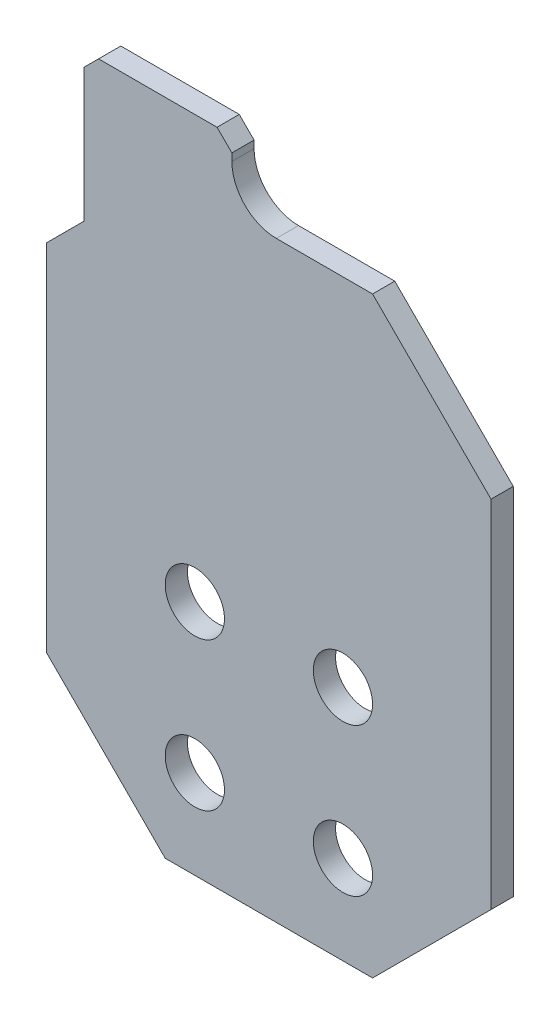
SolidWorks part; units mm, degrees
material "1060 Alloy"
ref_plane "Front Plane" through (0, 0, 0) normal (0, 0, 1) x (1, 0, 0)
ref_plane "Top Plane" through (0, 0, 0) normal (0, 1, 0) x (1, 0, 0)
ref_plane "Right Plane" through (0, 0, 0) normal (1, 0, 0) x (0, 0, -1)
sketch "Sketch1" plane through (0, 0, 0) normal (0, 0, 1) x (1, 0, 0)
  line L0 (20, -34) -> (10, -34) construction
  line L1 (0, 0) -> (30, 0)
  line L2 (0, 0) -> (0, -40)
  line L3 (0, -40) -> (30, -40)
  line L4 (30, 0) -> (30, -40)
  line L5 (10, -34) -> (15, -34) construction
  line L6 (15, -34) -> (15, -40) construction
  circle A0 centre (20, -34) radius 2
  circle A1 centre (10, -34) radius 2
  circle A2 centre (20, -24) radius 2
  circle A3 centre (10, -24) radius 2
  dimension "D1" = 4
  dimension "D2" = 4
  dimension "D3" = 6
  dimension "D4" = 10
  dimension "D5" = 40
  dimension "D6" = 30
  dimension "D7" = 10
extrude "Boss-Extrude1" add sketch "Sketch1" along normal blind 1.5
chamfer "Chamfer1" distance 8 angle 45 4 edges at (0, -40, 0.75) (30, -40, 0.75) (30, 0, 0.75) (0, 0, 0.75)
sketch "Sketch2" plane through (0, 0, 1.5) normal (0, 0, 1) x (1, 0, 0)
  line L0 (2.5, -5.5) -> (2.5, 4.5)
  line L1 (8, 0) -> (0, -8) construction
  line L2 (2.5, 4.5) -> (12.5, 4.5)
  line L3 (12.5, 4.5) -> (12.5, -5.5)
  line L4 (12.5, -5.5) -> (2.5, -5.5)
  dimension "D1" = 2.5
  dimension "D2" = 10
  dimension "D3" = 10
extrude "Boss-Extrude2" add sketch "Sketch2" against normal blind 1.5
ref_plane "Plane1" through (15, 0, 0) normal (1, 0, 0) x (0, 0, -1)
chamfer "Chamfer3" distance 1 angle 45 2 edges at (12.5, 4.5, 0.75) (2.5, 4.5, 0.75)
fillet "Fillet1" radius 3 1 edges at (12.5, 0, 0.75)
